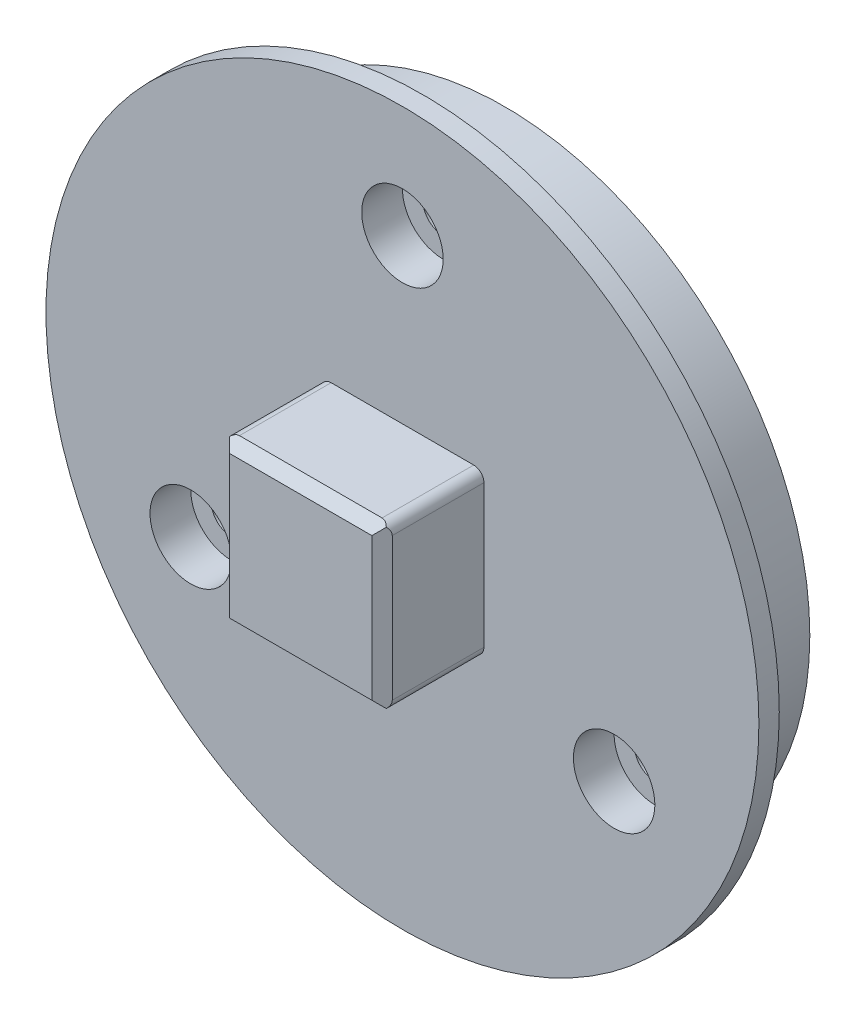
SolidWorks part; units mm, degrees
ref_plane "前视基准面" through (0, 0, 0) normal (0, 0, 1) x (1, 0, 0)
ref_plane "上视基准面" through (0, 0, 0) normal (0, 1, 0) x (1, 0, 0)
ref_plane "右视基准面" through (0, 0, 0) normal (1, 0, 0) x (0, 0, -1)
sketch "草图1" plane through (0, 0, 0) normal (0, 0, 1) x (1, 0, 0)
  circle A0 centre (0, 0) radius 10
  dimension "D1" = 20
extrude "凸台-拉伸1" add sketch "草图1" along normal blind 4
sketch "草图2" plane through (0, 0, 4) normal (0, 0, 1) x (1, 0, 0)
  circle A0 centre (0, 0) radius 11.5
  dimension "D1" = 23
extrude "凸台-拉伸2" add sketch "草图2" along normal blind 1
sketch "草图3" plane through (0, 0, 4) normal (0, 0, -1) x (-1, 0, 0)
  circle A0 centre (0, 0) radius 10.6
extrude "凸台-拉伸3" add sketch "草图3" along normal blind 0.4
sketch "草图9" plane through (0, 0, 0) normal (0, 0, -1) x (-1, 0, 0)
  circle A0 centre (0, 0) radius 5
  dimension "D1" = 10
extrude "切除-拉伸5" cut sketch "草图9" against normal blind 3
sketch "草图10" plane through (0, 0, 5) normal (0, 0, 1) x (1, 0, 0)
  circle A0 centre (0, 0) radius 11.5
  circle A1 centre (0, 0) radius 12.5
  dimension "D1" = 25
extrude "凸台-拉伸4" add sketch "草图10" against normal up to surface (1 mm away) up to face at (10.6, 0, 4)
sketch "草图11" plane through (0, 0, 3) normal (0, 0, -1) x (-1, 0, 0)
  circle A0 centre (0, 0) radius 5
  circle A1 centre (0, 0) radius 4
  dimension "D1" = 8
extrude "凸台-拉伸5" add sketch "草图11" along normal up to surface (3 mm away) up to face at (-5, 0, 0)
sketch "草图12" plane through (0, 0, 3) normal (0, 0, -1) x (-1, 0, 0)
  circle A0 centre (0, 0) radius 4
  circle A1 centre (0, 0) radius 2
  dimension "D1" = 4
extrude "切除-拉伸6" cut sketch "草图12" against normal blind 1.1
sketch "草图15" plane through (0, 0, 5) normal (0, 0, 1) x (1, 0, 0)
  circle A0 centre (0, 0) radius 17.5
  dimension "D1" = 35
extrude "凸台-拉伸7" add sketch "草图15" against normal up to surface (1 mm away) up to face at (10.6, 0, 4)
sketch "草图16" plane through (0, 0, 4) normal (0, 0, -1) x (-1, 0, 0)
  circle A0 centre (0, 0) radius 15
  circle A2 centre (0, 0) radius 4
  dimension "D1" = 30
extrude "凸台-拉伸9" add sketch "草图16" along normal up to surface (4 mm away) up to face at (10, 0, 0)
sketch "草图17" plane through (0, 0, 0) normal (0, 0, -1) x (-1, 0, 0)
  line L0 (0, 0) -> (0, 12) construction
  circle A0 centre (0, 12) radius 1
  circle A1 centre (10.3923, 6) radius 1
  circle A2 centre (10.3923, -6) radius 1
  circle A3 centre (0, -12) radius 1
  circle A4 centre (-10.3923, -6) radius 1
  circle A5 centre (-10.3923, 6) radius 1
  point P16 (0, 0)
  dimension "D2" = 2
  dimension "D1" = 12
  dimension "D3" = 6
extrude "切除-拉伸8" cut sketch "草图17" against normal blind 2.6
sketch "草图18" plane through (0, 0, 4) normal (0, 0, -1) x (-1, 0, 0)
  circle A0 centre (0, 0) radius 15
  circle A1 centre (0, 0) radius 15.5
extrude "凸台-拉伸10" add sketch "草图18" along normal blind 0.4
sketch "草图19" plane through (0, 0, 2.6) normal (0, 0, -1) x (-1, 0, 0)
  circle A0 centre (0, 12) radius 1
  circle A1 centre (10.3923, -6) radius 1
  circle A2 centre (-10.3923, -6) radius 1
  point P9 (0, 0)
  dimension "D1" = 3
extrude "切除-拉伸9" cut sketch "草图19" against normal through all both and the other way through all
sketch "草图20" plane through (0, 0, 5) normal (0, 0, 1) x (1, 0, 0)
  circle A0 centre (0, 12) radius 2
  circle A1 centre (10.3923, -6) radius 2
  circle A2 centre (-10.3923, -6) radius 2
  point P9 (0, 0)
  dimension "D1" = 4
  dimension "D2" = 3
extrude "切除-拉伸10" cut sketch "草图20" against normal blind 2
sketch "草图21" plane through (0, 0, 3.6) normal (0, 0, -1) x (-1, 0, 0)
  circle A0 centre (0, 0) radius 15.5
  circle A1 centre (0, 0) radius 16.5
  dimension "D1" = 1
extrude "凸台-拉伸11" add sketch "草图21" against normal up to surface (0.4 mm away) up to face at (17.5, 0, 4)
sketch "草图27" plane through (0, 0, 0) normal (0, 0, -1) x (-1, 0, 0)
  circle A0 centre (0, 0) radius 4
extrude "凸台-拉伸12" add sketch "草图27" against normal up to surface (4 mm away) up to face at (4, 0, 4)
sketch "草图38" plane through (0, 0, 2.6) normal (0, 0, -1) x (-1, 0, 0)
  circle A0 centre (10.3923, 6) radius 1
  circle A1 centre (0, -12) radius 1
  circle A2 centre (-10.3923, 6) radius 1
  point P9 (0, 0)
  dimension "D1" = 3
extrude "凸台-拉伸16" add sketch "草图38" along normal blind 0.5
sketch "草图40" plane through (0, 0, 5) normal (0, 0, 1) x (1, 0, 0)
  line L1 (4, -4) -> (-4, -4)
  line L2 (4, -4) -> (4, 4)
  line L3 (4, 4) -> (-4, 4)
  line L4 (-4, -4) -> (-4, 4)
  line L5 (4, -4) -> (-4, 4) construction
  line L6 (4, 4) -> (-4, -4) construction
  point P0 (0, 0)
  dimension "D1" = 8
  dimension "D2" = 8
extrude "凸台-拉伸18" add sketch "草图40" along normal blind 5
chamfer "倒角1" distance 0.5 angle 45 4 edges at (0, 4, 10) (4, 0, 10) (0, -4, 10) (-4, 0, 10)
fillet "圆角1" radius 0.5 4 edges at (-4, 4, 7.25) (4, 4, 7.25) (4, -4, 7.25) (-4, -4, 7.25)
sketch "草图41" plane through (0, 0, 0) normal (0, 0, -1) x (-1, 0, 0)
  circle A0 centre (0, 0) radius 2.5
  dimension "D1" = 5
extrude "切除-拉伸11" cut sketch "草图41" against normal blind 3.1
